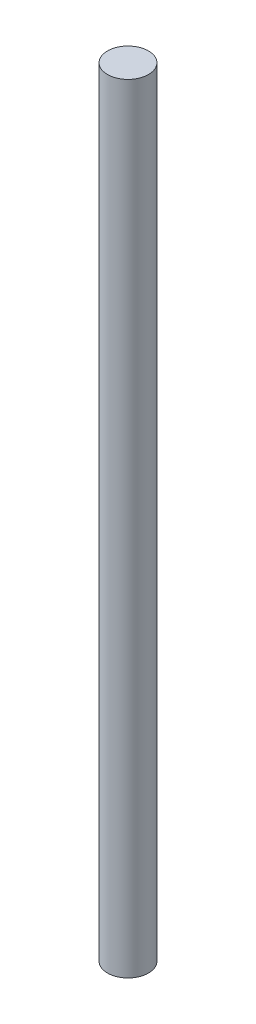
SolidWorks part; units mm, degrees
ref_plane "前视基准面" through (0, 0, 0) normal (0, 0, 1) x (1, 0, 0)
ref_plane "上视基准面" through (0, 0, 0) normal (0, 1, 0) x (1, 0, 0)
ref_plane "右视基准面" through (0, 0, 0) normal (1, 0, 0) x (0, 0, -1)
sketch "草图1" plane through (0, 0, 0) normal (0, 1, 0) x (1, 0, 0)
  circle A0 centre (0, 0) radius 5
  dimension "D1" = 10
extrude "凸台-拉伸1" add sketch "草图1" along normal blind 190
